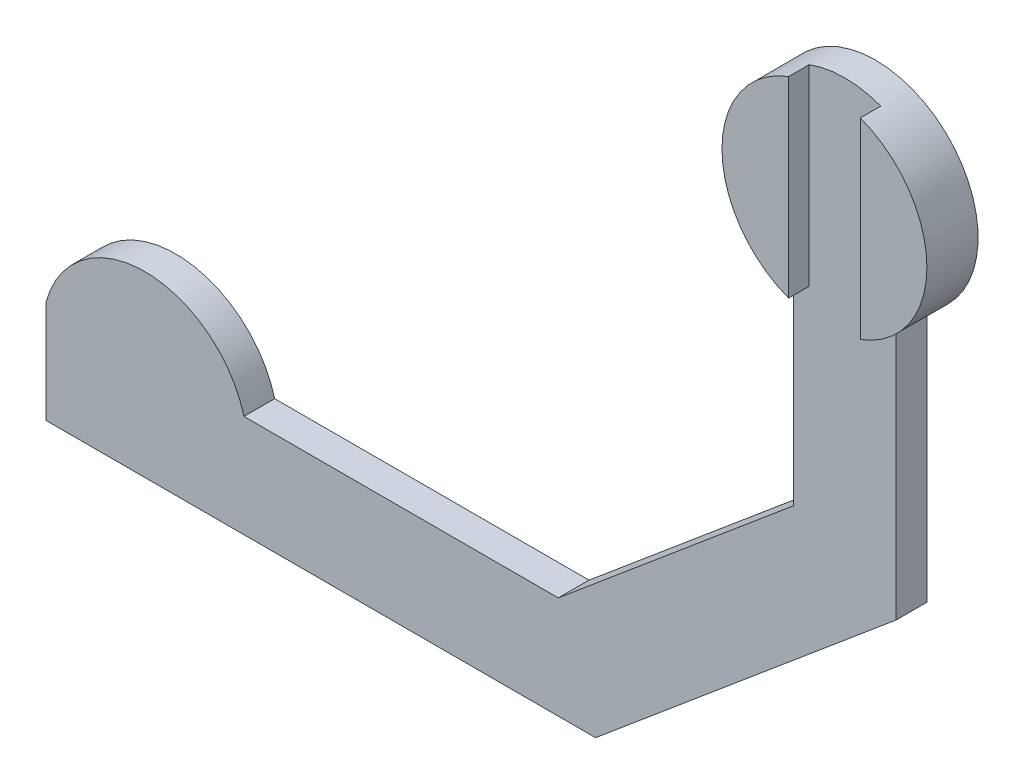
SolidWorks part; units mm, degrees
ref_plane "Front Plane" through (0, 0, 0) normal (0, 0, 1) x (1, 0, 0)
ref_plane "Top Plane" through (0, 0, 0) normal (0, 1, 0) x (1, 0, 0)
ref_plane "Right Plane" through (0, 0, 0) normal (1, 0, 0) x (0, 0, -1)
sketch "Sketch2" plane through (0, 0, 0) normal (0, 0, 1) x (1, 0, 0)
  circle A0 centre (0, 0) radius 10
  dimension "D1" = 20
extrude "Boss-Extrude1" add sketch "Sketch2" along normal blind 3
sketch "Sketch3" plane through (0, 0, 3) normal (0, 0, 1) x (1, 0, 0)
  line L0 (5, -8.6603) -> (-5, -8.6603) construction
  line L1 (-5, -8.6603) -> (5, -8.6603)
  line L2 (5, -8.6603) -> (5, -33.3233)
  line L3 (5, -33.3233) -> (-24.3416, -57.9439)
  line L4 (-24.3416, -57.9439) -> (-77.9813, -57.9439)
  line L5 (-77.9813, -57.9439) -> (-77.9813, -47.9439)
  line L6 (-77.9813, -47.9439) -> (-27.9813, -47.9439)
  line L7 (-27.9813, -47.9439) -> (-5, -28.6603)
  line L8 (-5, -28.6603) -> (-5, -8.6603)
  circle A0 centre (0, 0) radius 10 construction
  point P10 (5, -42.6014)
  dimension "D1" = 10
  dimension "D2" = 10
  dimension "D3" = 10
  dimension "D4" = 30
  dimension "D5" = 50
  dimension "D6" = 20
  dimension "D7" = 220
extrude "Boss-Extrude2" add sketch "Sketch3" against normal blind 3
sketch "Sketch4" plane through (0, 0, 3) normal (0, 0, 1) x (1, 0, 0)
  line L1 (-77.9813, -47.9439) -> (-58.6628, -47.9439)
  arc A0 (-77.9813, -47.9439) -> (-58.6628, -47.9439) centre (-68.3221, -50.5321) cw
  point P3 (0, 0)
  point P7 (0, 0)
  dimension "D1" = 10
extrude "Boss-Extrude3" add sketch "Sketch4" against normal blind 3
sketch "Sketch5" plane through (0, 0, 3) normal (0, 0, 1) x (1, 0, 0)
  line L0 (0, 10) -> (0, -8.7502) construction
  line L2 (-3.5, 9.3675) -> (-3.5, -9.3675)
  line L4 (3.5, 9.3675) -> (3.5, -9.3675)
  arc A0 (3.5, -9.3675) -> (3.5, 9.3675) centre (0, 0) ccw
  arc A1 (3.5, -9.3675) -> (3.5, 9.3675) centre (0, 0) ccw
  arc A2 (-3.5, 9.3675) -> (-3.5, -9.3675) centre (0, 0) ccw
  arc A3 (-3.5, 9.3675) -> (-3.5, -9.3675) centre (0, 0) ccw
  arc A4 (5, -8.6603) -> (-5, -8.6603) centre (0, 0) ccw construction
  arc M6 (5, -8.6603) -> (-5, -8.6603) centre (0, 0) ccw
  dimension "D1" = 7
extrude "Boss-Extrude7" add sketch "Sketch5" along normal blind 2 contours A2 L2 M6 | L4 A0 M6
